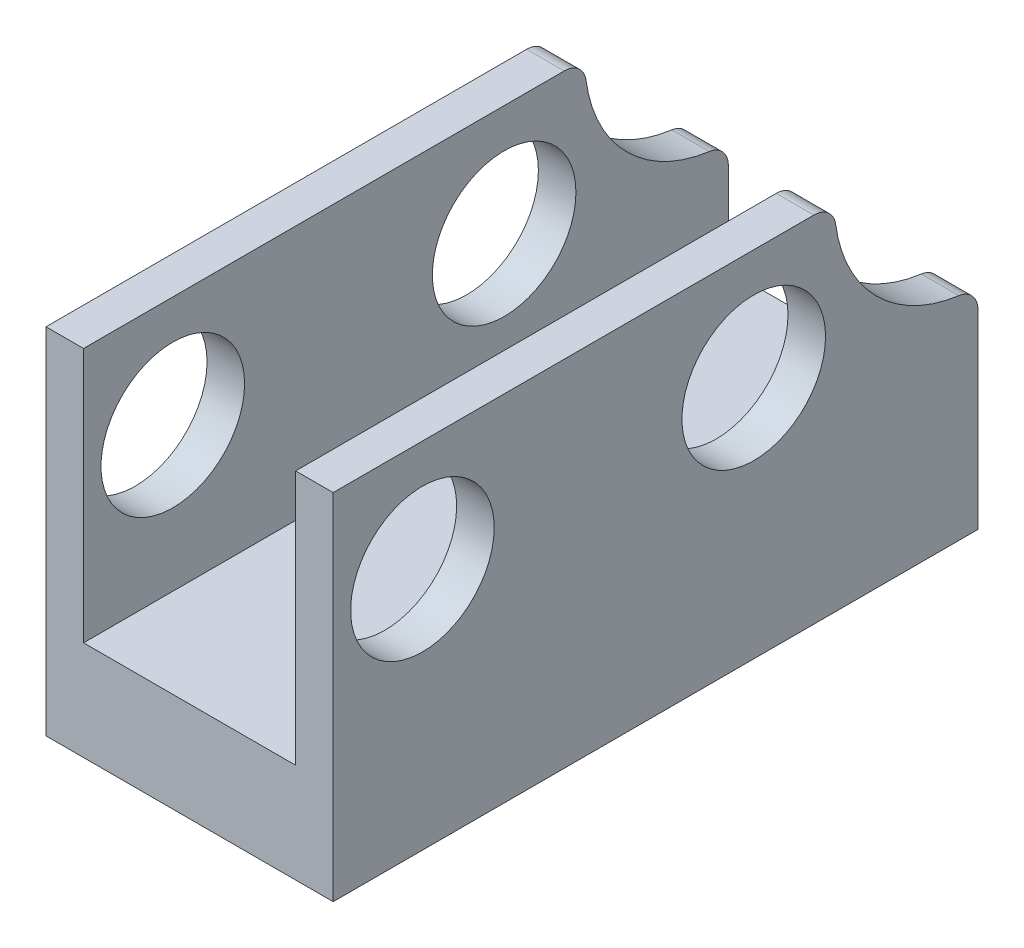
SolidWorks part; units mm, degrees
ref_plane "Front" through (0, 0, 0) normal (0, 0, 1) x (1, 0, 0)
ref_plane "Top" through (0, 0, 0) normal (0, 1, 0) x (1, 0, 0)
ref_plane "Right" through (0, 0, 0) normal (1, 0, 0) x (0, 0, -1)
sketch "Sketch1" plane through (0, 0, 0) normal (1, 0, 0) x (0, 0, -1)
  line L1 (-7.2978, 4.01) -> (7.2978, 4.01)
  line L2 (-7.2978, 4.01) -> (-7.2978, -4.01)
  line L3 (-7.2978, -4.01) -> (7.2978, -4.01)
  line L4 (7.2978, 4.01) -> (7.2978, -4.01)
  circle A0 centre (-5.2778, 1.5) radius 1.625
  circle A1 centre (2.2222, 1.5) radius 1.625
  point P4 (0, 4.01)
  point P6 (7.2978, 0)
  dimension "D3" = 3.25
  dimension "D1" = 8.02
  dimension "D2" = 14.5956
  dimension "D4" = 2.02
  dimension "D5" = 5.51
  dimension "D6" = 7.5
extrude "Boss-Extrude1" add sketch "Sketch1" along normal mid plane 6.5
sketch "Sketch2" plane through (0, 0, 0) normal (1, 0, 0) x (0, 0, -1)
  line L0 (-7.2978, -4.01) -> (7.2978, -4.01) construction
  line L1 (-7.2978, 4.01) -> (7.2978, 4.01)
  line L2 (-7.2978, 4.01) -> (-7.2978, -1.76)
  line L3 (-7.2978, -1.76) -> (7.2978, -1.76)
  line L4 (7.2978, 4.01) -> (7.2978, -1.76)
  line L5 (7.2978, -4.01) -> (7.2978, 4.01) construction
  dimension "D1" = 2.25
extrude "Cut-Extrude1" cut sketch "Sketch2" against normal mid plane 4.8
sketch "Sketch4" plane through (0, 0, 0) normal (1, 0, 0) x (0, 0, -1)
  line L0 (4.0478, 4.8559) -> (4.0478, -0.4609) construction
  line L1 (4.1801, 0.76) -> (10.0808, 0.76) construction
  line L2 (7.2978, 4.01) -> (-7.2978, 4.01) construction
  line L3 (7.2978, -4.01) -> (7.2978, 4.01) construction
  line L4 (4.0478, 4.01) -> (7.2978, 4.01)
  line L5 (7.2978, 4.01) -> (7.2978, 0.76)
  arc A0 (4.0478, 4.01) -> (7.2978, 0.76) centre (7.2978, 4.01) ccw
  dimension "D1" = 3.25
extrude "Cut-Extrude2" cut sketch "Sketch4" against normal through all and the other way through all
fillet "Fillet1" radius 0.5 4 edges at (2.825, 0.76, -7.2978) (2.825, 4.01, -4.0478) (-2.825, 0.76, -7.2978) (-2.825, 4.01, -4.0478)
